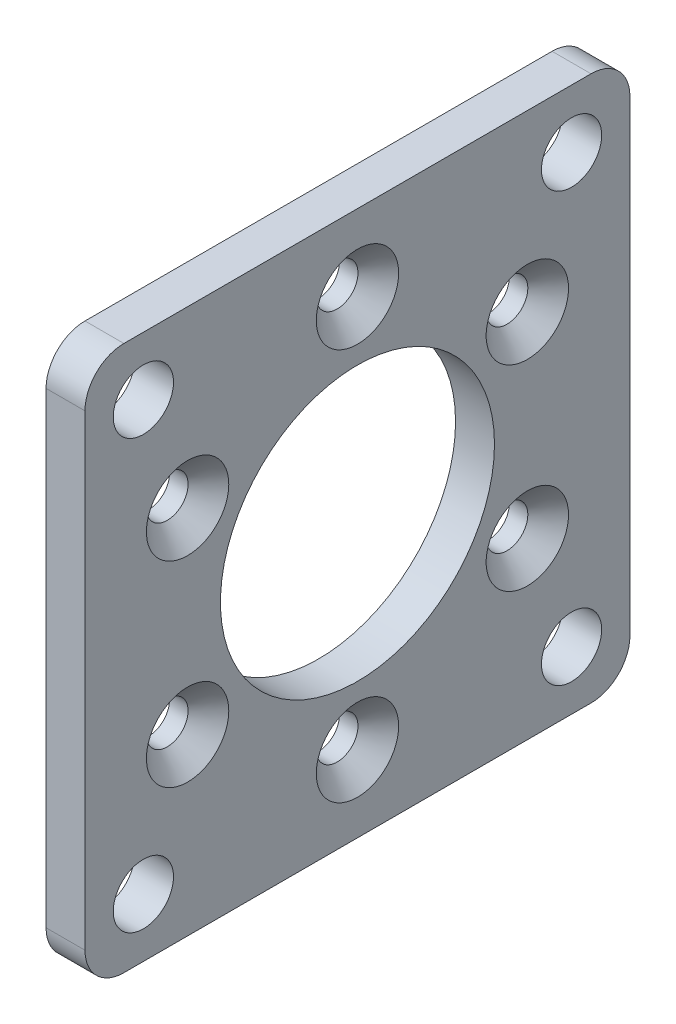
SolidWorks part; units mm, degrees
material "6061-T6 (SS)"
ref_plane "Front" through (0, 0, 0) normal (0, 0, 1) x (1, 0, 0)
ref_plane "Top" through (0, 0, 0) normal (0, 1, 0) x (1, 0, 0)
ref_plane "Right" through (0, 0, 0) normal (1, 0, 0) x (0, 0, -1)
sketch "Sketch1" plane through (0, 0, 0) normal (1, 0, 0) x (0, 0, -1)
  line L1 (22.225, -22.225) -> (-22.225, -22.225)
  line L2 (22.225, -22.225) -> (22.225, 22.225)
  line L3 (22.225, 22.225) -> (-22.225, 22.225)
  line L4 (-22.225, -22.225) -> (-22.225, 22.225)
  line L5 (22.225, -22.225) -> (-22.225, 22.225) construction
  line L6 (22.225, 22.225) -> (-22.225, -22.225) construction
  circle A0 centre (0, 0) radius 11.176
  dimension "D1" = 22.352
  dimension "D2" = 44.45
  dimension "D3" = 44.45
extrude "Boss-Extrude1" add sketch "Sketch1" along normal blind 3.175
sketch "Sketch4" plane through (3.175, 0, 0) normal (1, 0, 0) x (0, 0, -1)
  line L1 (22.225, 22.225) -> (-22.225, 22.225) construction
  line L2 (-22.225, 22.225) -> (-22.225, -22.225) construction
  line L3 (22.225, -22.225) -> (22.225, 22.225) construction
  line L4 (-22.225, -22.225) -> (22.225, -22.225) construction
  point P0 (-17.4625, 17.4625)
  point P2 (17.4625, 17.4625)
  point P4 (17.4625, -17.4625)
  point P6 (-17.4625, -17.4625)
  dimension "D1" = 4.7625
  dimension "D2" = 4.7625
  dimension "D3" = 4.7625
  dimension "D4" = 4.7625
hole_wizard "#10 (0.1935) Diameter Hole1" positions "Sketch4" profile "Sketch3" hole size "#10" standard "ANSI Inch" end condition up to next
sketch "Sketch3" plane through (3.175, 17.4625, 17.4625) normal (0, 1, 0) x (0, 0, -1)
  line L0 (0, 0) -> (0, 3.175)
  line L1 (0, 3.175) -> (2.4574, 3.175)
  line L2 (2.4574, 3.175) -> (2.4574, 0)
  line L5 (2.4574, 0) -> (0, 0)
  line L11 (0, -6.35) -> (0, 107.95) construction
  dimension "Thru Hole Dia." = 4.9149
  dimension "Thru Hole Depth" = 3.175
sketch "Sketch7" plane through (3.175, 0, 0) normal (1, 0, 0) x (0, 0, -1)
  circle A0 centre (0, 0) radius 16 construction
  point P5 (0, 16)
  point P11 (13.8564, 8)
  point P12 (13.8564, -8)
  point P13 (0, -16)
  point P14 (-13.8564, -8)
  point P15 (-13.8564, 8)
  dimension "D2" = 32
  dimension "D1" = 6
hole_wizard "CSK for M3 SFHCS1" positions "Sketch7" profile "Sketch6" countersink size "M3" standard "ANSI Metric" end condition up to next
sketch "Sketch6" plane through (3.175, 8, 13.8564) normal (0, 1, 0) x (0, 0, -1)
  line L0 (0, 0) -> (0, 3.175)
  line L1 (0, 3.175) -> (1.7, 3.175)
  line L2 (1.7, 3.175) -> (1.7, 1.66)
  line L3 (1.7, 1.66) -> (3.36, 0)
  line L5 (3.36, 0) -> (0, 0)
  line L6 (-1.7, 1.66) -> (-3.36, 0) construction
  line L11 (0, -6.35) -> (0, 107.95) construction
  dimension "Thru Hole Dia." = 3.4
  dimension "Thru Hole Depth" = 3.175
  dimension "Near C'Sink Dia." = 6.72
  dimension "Near C'Sink Angle" = 90
fillet "Fillet1" radius 3.175 4 edges at (1.5875, 22.225, 22.225) (1.5875, 22.225, -22.225) (1.5875, -22.225, -22.225) (1.5875, -22.225, 22.225)
